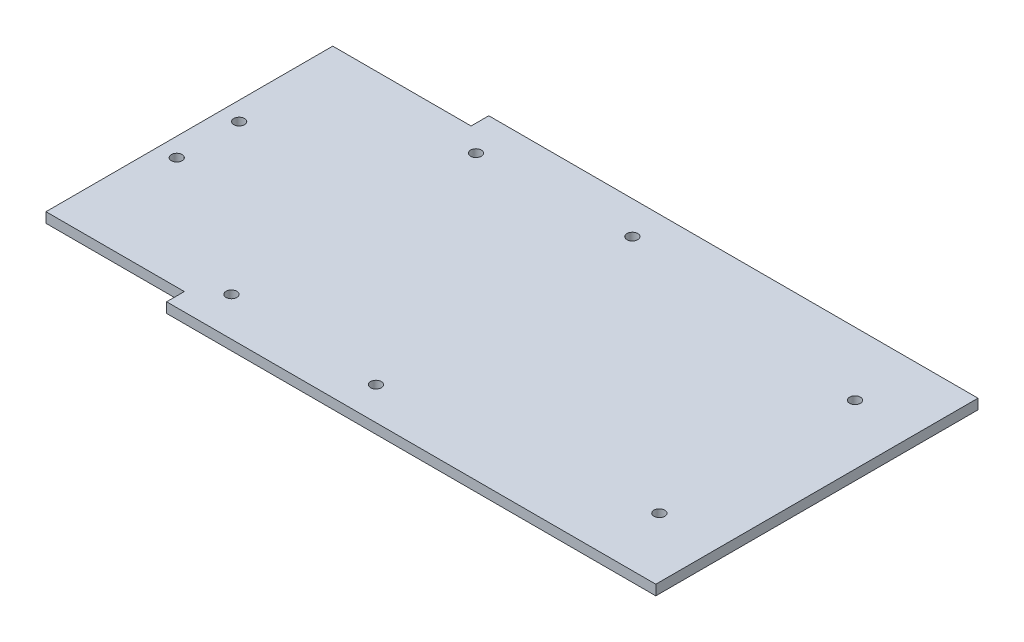
SolidWorks part; units mm, degrees
ref_plane "Front Plane" through (0, 0, 0) normal (0, 0, 1) x (1, 0, 0)
ref_plane "Top Plane" through (0, 0, 0) normal (0, 1, 0) x (1, 0, 0)
ref_plane "Right Plane" through (0, 0, 0) normal (1, 0, 0) x (0, 0, -1)
sketch "Sketch1" plane through (0, 0, 0) normal (0, 1, 0) x (1, 0, 0)
  line L0 (41, 5.25) -> (41, 0)
  line L5 (0, 90.25) -> (41, 90.25)
  line L6 (0, 90.25) -> (0, 5.25)
  line L7 (0, 5.25) -> (41, 5.25)
  line L9 (41, 95.5) -> (186, 95.5)
  line L10 (41, 95.5) -> (41, 90.25)
  line L11 (41, 0) -> (186, 0)
  line L12 (186, 95.5) -> (186, 0)
  point P0 (0, 47.75)
  point P2 (186, 47.75)
  dimension "D1" = 186
  dimension "D2" = 95.5
  dimension "D3" = 85
  dimension "D4" = 41
extrude "Boss-Extrude1" add sketch "Sketch1" along normal blind 3
sketch "Sketch2" plane through (0, 3, 0) normal (0, 1, 0) x (1, 0, 0)
  line L1 (0, 90.25) -> (0, 5.25) construction
  line L2 (5.5, 57) -> (5.5, 38.5) construction
  line L3 (0, 47.75) -> (186, 47.75) construction
  line L4 (186, 0) -> (186, 95.5) construction
  circle A0 centre (5.5, 38.5) radius 1.6
  circle A4 centre (5.5, 57) radius 1.6
  circle A5 centre (48.7, 11.5) radius 1.6
  circle A6 centre (93.3, 9.75) radius 1.6
  circle A7 centre (168.3, 18.75) radius 1.6
  circle A8 centre (168.3, 76.75) radius 1.6
  circle A9 centre (93.3, 85.75) radius 1.6
  circle A10 centre (48.7, 84) radius 1.6
  point P20 (0, 47.75)
  point P21 (5.5, 47.75)
  dimension "D1" = 3.2
  dimension "D2" = 3.2
  dimension "D3" = 48.7
  dimension "D4" = 93.3
  dimension "D5" = 75
  dimension "D6" = 3.2
  dimension "D7" = 3.2
  dimension "D8" = 3.2
  dimension "D9" = 72.5
  dimension "D11" = 58
  dimension "D10" = 76
  dimension "D12" = 5.5
  dimension "D13" = 5.5
  dimension "D14" = 18.5
extrude "Cut-Extrude1" cut sketch "Sketch2" against normal through all
sketch "Sketch3" plane through (0, 3, 0) normal (0, 1, 0) x (1, 0, 0)
  line L0 (0, 47.75) -> (186, 47.75) construction
  line L1 (0, 90.25) -> (0, 5.25) construction
  line L2 (186, 0) -> (186, 95.5) construction
